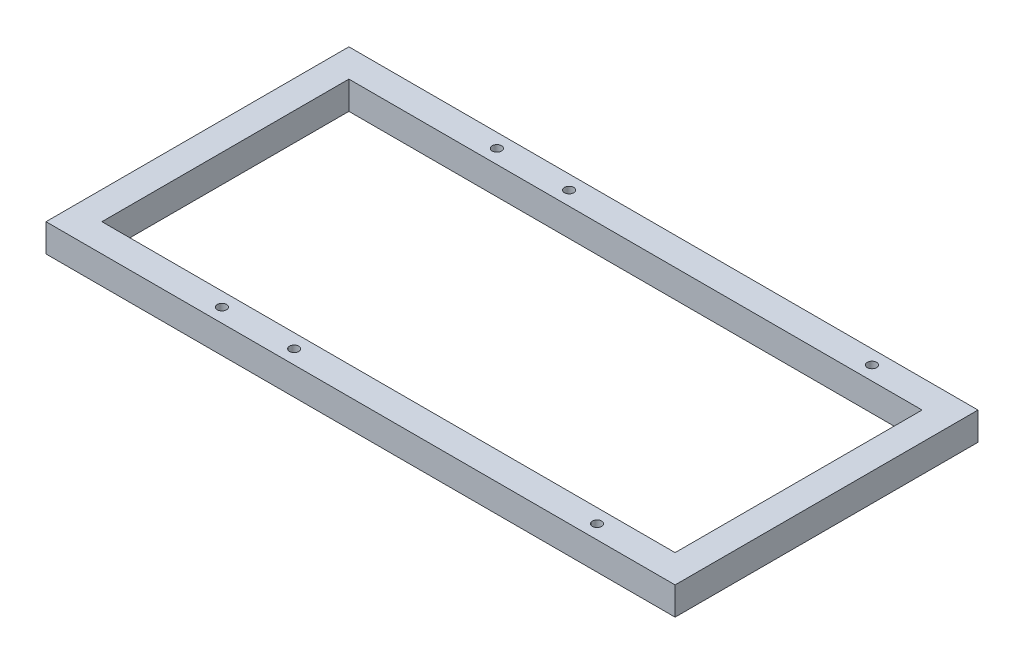
SolidWorks part; units mm, degrees
material "1060 Alloy"
ref_plane "Front Plane" through (0, 0, 0) normal (0, 0, 1) x (1, 0, 0)
ref_plane "Top Plane" through (0, 0, 0) normal (0, 1, 0) x (1, 0, 0)
ref_plane "Right Plane" through (0, 0, 0) normal (1, 0, 0) x (0, 0, -1)
sketch "Sketch1" plane through (0, 0, 0) normal (0, 1, 0) x (1, 0, 0)
  line L0 (110.0769, -53) -> (135, -65) construction
  line L1 (-135, 65) -> (135, 65)
  line L2 (-135, 65) -> (-135, -65)
  line L3 (-135, -65) -> (135, -65)
  line L4 (135, 65) -> (135, -65)
  line L5 (-135, 65) -> (-110.0769, 53) construction
  line L6 (-135, -65) -> (-110.0769, -53) construction
  line L7 (-123, 53) -> (123, 53)
  line L8 (-123, 53) -> (-123, -53)
  line L9 (-123, -53) -> (123, -53)
  line L10 (123, 53) -> (123, -53)
  line L13 (110.0769, 53) -> (135, 65) construction
  point P0 (0, 0)
  point P6 (0, 0)
  dimension "D1" = 270
  dimension "D2" = 130
  dimension "D3" = 106
  dimension "D4" = 246
extrude "Boss-Extrude1" add sketch "Sketch1" along normal blind 12
sketch "Sketch3" plane through (0, 12, 0) normal (0, 1, 0) x (1, 0, 0)
  line L0 (-135, -65) -> (135, -65) construction
  line L2 (-135, 65) -> (-135, -65) construction
  circle A0 centre (-65.5, -59) radius 2
  dimension "D3" = 4
  dimension "D1" = 6
  dimension "D2" = 69.5
extrude "Cut-Extrude1" cut sketch "Sketch3" against normal blind 50.25
mirror "Mirror1" about plane through (0, 0, 0) normal (0, 0, 1) of "Cut-Extrude1"
pattern_linear "LPattern1" count 2 spacing 31 along (1, 0, 0) of "Mirror1", "Cut-Extrude1"
pattern_linear "LPattern2" count 2 spacing 161 along (1, 0, 0) of "Cut-Extrude1"
mirror "Mirror2" about plane through (0, 0, 0) normal (0, 0, 1) of "LPattern2"
